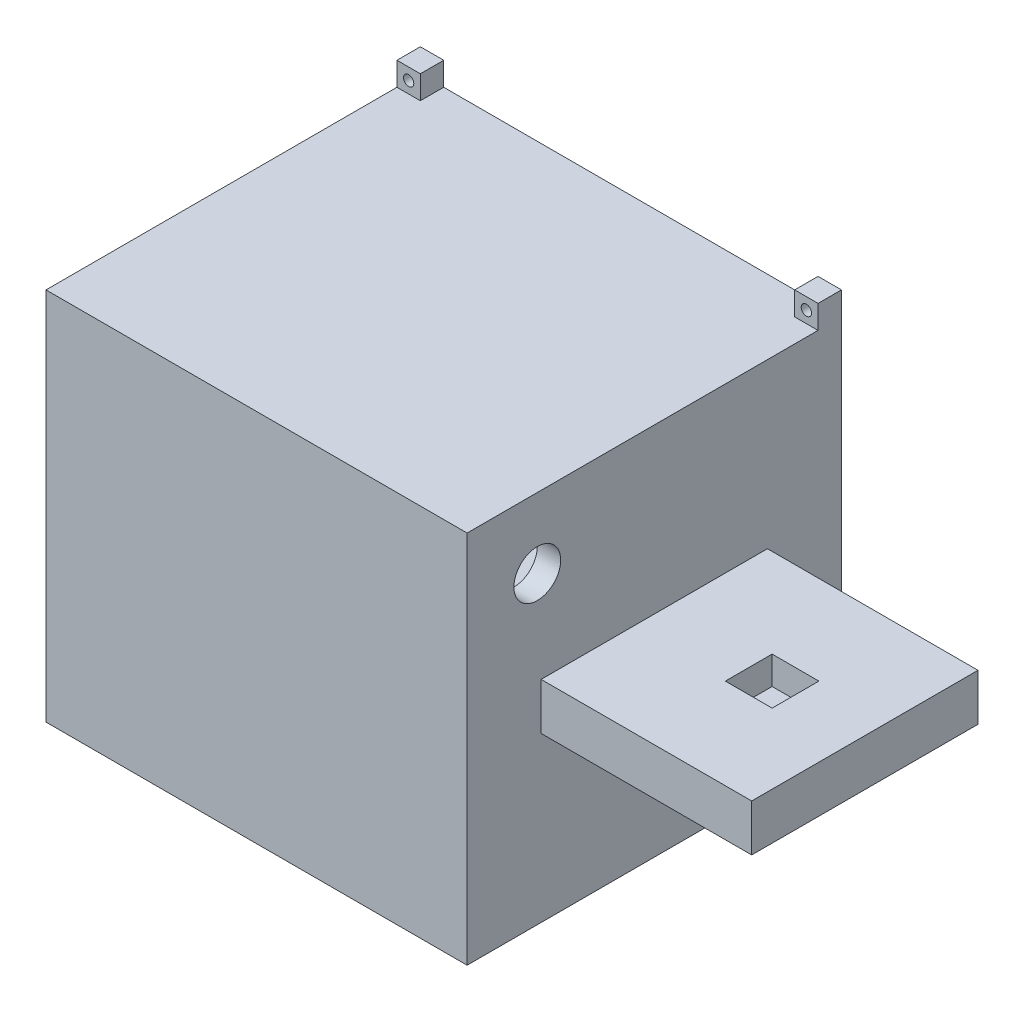
SolidWorks part; units mm, degrees
ref_plane "前基準面" through (0, 0, 0) normal (0, 0, 1) x (1, 0, 0)
ref_plane "上基準面" through (0, 0, 0) normal (0, 1, 0) x (1, 0, 0)
ref_plane "右基準面" through (0, 0, 0) normal (1, 0, 0) x (0, 0, -1)
sketch "草圖1" plane through (0, 0, 0) normal (0, 0, 1) x (1, 0, 0)
  line L0 (-75.5089, 45.5899) -> (59.4911, 45.5899)
  line L4 (-75.5089, 5.5899) -> (59.4911, 5.5899) construction
  line L5 (-75.5089, 45.5899) -> (-75.5089, -34.4101)
  line L6 (59.4911, 45.5899) -> (59.4911, -34.4101)
  line L7 (-75.5089, -34.4101) -> (59.4911, -34.4101)
  dimension "D1" = 135
  dimension "D2" = 80
extrude "填料-伸長1" add sketch "草圖1" along normal blind 80
sketch "草圖5" plane through (0, -34.4101, 0) normal (0, -1, 0) x (1, 0, 0)
  line L0 (14.4911, 80) -> (14.4911, 0)
  line L1 (-75.5089, 80) -> (59.4911, 80) construction
  line L2 (-75.5089, 0) -> (59.4911, 0) construction
  line L3 (14.4911, 0) -> (59.4911, 0)
  line L4 (59.4911, 0) -> (59.4911, 80)
  line L5 (59.4911, 80) -> (14.4911, 80)
  dimension "D1" = 45
sketch "草圖6" plane through (0, 45.5899, 0) normal (0, 1, 0) x (1, 0, 0)
  line L0 (14.4911, 0) -> (14.4911, -80)
  line L1 (14.4911, -80) -> (59.4911, -80)
  line L2 (59.4911, -80) -> (59.4911, 0)
  line L3 (59.4911, 0) -> (14.4911, 0)
extrude "除料-伸長1" cut sketch "草圖6" against normal blind 35
extrude "除料-伸長2" cut sketch "草圖5" against normal blind 35
sketch "草圖7" plane through (0, 0, 0) normal (0, 0, 1) x (1, 0, 0)
  line L0 (-75.5089, 5.5899) -> (59.4911, 5.5899) construction
  line L1 (-75.5089, 45.5899) -> (-75.5089, -34.4101) construction
  line L2 (59.4911, 0.5899) -> (59.4911, 10.5899) construction
  line L3 (-70.5089, -29.4101) -> (-70.5089, 40.5899)
  line L4 (-70.5089, 40.5899) -> (9.4911, 40.5899)
  line L5 (9.4911, 40.5899) -> (9.4911, -29.4101)
  line L6 (-70.5089, -29.4101) -> (9.4911, -29.4101)
  line L7 (14.4911, 45.5899) -> (-75.5089, 45.5899) construction
  line L8 (14.4911, 0.5899) -> (14.4911, -34.4101) construction
  point P11 (9.4911, 5.5899)
  point P12 (-70.5089, 5.5899)
  dimension "D1" = 5
  dimension "D2" = 5
  dimension "D3" = 5
extrude "除料-伸長3" cut sketch "草圖7" along normal blind 75
sketch "草圖8" plane through (0, 0, 0) normal (0, 0, -1) x (-1, 0, 0)
  line L0 (-59.4911, 5.5899) -> (75.5089, 5.5899) construction
  line L1 (-59.4911, 0.5899) -> (-59.4911, 10.5899) construction
  line L2 (75.5089, 45.5899) -> (75.5089, -34.4101) construction
  line L3 (-13.3911, 44.4899) -> (-13.3911, -33.3101)
  line L4 (-13.3911, 44.4899) -> (74.4089, 44.4899)
  line L5 (74.4089, 44.4899) -> (74.4089, -33.3101)
  line L7 (71.6089, -30.5101) -> (71.6089, 41.6899)
  line L8 (71.6089, 41.6899) -> (-10.5911, 41.6899)
  line L9 (-10.5911, 41.6899) -> (-10.5911, -30.5101)
  line L11 (-14.4911, 45.5899) -> (75.5089, 45.5899) construction
  line L12 (-14.4911, 10.5899) -> (-14.4911, 45.5899) construction
  line L13 (71.6089, -30.5101) -> (-10.5911, -30.5101)
  line L14 (-13.3911, -33.3101) -> (74.4089, -33.3101)
  dimension "D1" = 2.8
  dimension "D2" = 2.8
  dimension "D3" = 2.8
  dimension "D4" = 1.1
  dimension "D5" = 1.1
  dimension "D6" = 1.1
extrude "除料-伸長4" cut sketch "草圖8" against normal blind 10
ref_plane "平面1" through (14.4911, 0, 0) normal (1, 0, 0) x (0, 0, -1)
sketch "草圖9" plane through (14.4911, 0, 0) normal (1, 0, 0) x (0, 0, -1)
  line L0 (-80, 5.5899) -> (0, 5.5899) construction
  line L1 (-80, 0.5899) -> (-80, 10.5899) construction
  line L2 (0, 0.5899) -> (0, 10.5899) construction
  line L3 (0, 41.6899) -> (0, -30.5101) construction
  line L4 (-80, 10.5899) -> (-80, 45.5899) construction
  line L5 (0, 10.5899) -> (-80, 10.5899) construction
  line L6 (0, 0.5899) -> (-80, 0.5899) construction
  circle A2 centre (-65, 30.5899) radius 5
  circle A3 centre (-20, -19.4101) radius 5
  dimension "D1" = 10
  dimension "D2" = 10
  dimension "D3" = 20
  dimension "D4" = 15
  dimension "D5" = 20
  dimension "D6" = 20
extrude "除料-伸長5" cut sketch "草圖9" against normal blind 32.4
ref_plane "平面2" through (0, -34.4101, 0) normal (0, -1, 0) x (-1, 0, 0)
sketch "草圖10" plane through (0, -34.4101, 0) normal (0, -1, 0) x (-1, 0, 0)
  line L0 (75.5089, 0) -> (-14.4911, 0) construction
  line L1 (14.0089, -15) -> (35.5089, -15)
  line L2 (14.0089, -15) -> (14.0089, -30)
  line L3 (14.0089, -30) -> (35.5089, -30)
  line L4 (35.5089, -15) -> (35.5089, -30)
  line L5 (75.5089, -80) -> (75.5089, 0) construction
  point P6 (24.7589, -15)
  dimension "D1" = 21.5
  dimension "D2" = 15
  dimension "D3" = 15
  dimension "D4" = 40
extrude "除料-伸長6" cut sketch "草圖10" against normal blind 10
sketch "草圖12" plane through (14.4911, 0, 0) normal (1, 0, 0) x (0, 0, -1)
  line L0 (-40, 45.5899) -> (-40, -34.4101) construction
  line L1 (0, 45.5899) -> (-80, 45.5899) construction
  line L2 (-80, -34.4101) -> (0, -34.4101) construction
  line L3 (-80, 10.5899) -> (-80, 0.5899)
  line L4 (-80, 0.5899) -> (-64.1831, 0.5899)
  line L5 (0, 0.5899) -> (-80, 0.5899) construction
  line L6 (-64.1831, 0.5899) -> (-64.1831, 10.5899)
  line L7 (0, 10.5899) -> (-80, 10.5899) construction
  line L8 (-64.1831, 10.5899) -> (-80, 10.5899)
  line L9 (-15.8169, 10.5899) -> (0, 10.5899)
  line L10 (0, 10.5899) -> (0, 0.5899)
  line L11 (0, 0.5899) -> (-15.8169, 0.5899)
  line L12 (-15.8169, 0.5899) -> (-15.8169, 10.5899)
extrude "除料-伸長7" cut sketch "草圖12" along normal blind 45
ref_plane "平面3" through (0, 0.5899, 0) normal (0, -1, 0) x (-1, 0, 0)
sketch "草圖14" plane through (0, 0.5899, 0) normal (0, -1, 0) x (-1, 0, 0)
  line L4 (-59.4911, -40) -> (-70.9929, -40) construction
  line L5 (-59.4911, -15.8169) -> (-59.4911, -64.1831) construction
  line L6 (-38.0091, -35.1028) -> (-21.5179, -38.5)
  line L7 (-38.0091, -44.8972) -> (-21.5179, -41.5)
  line L8 (-39.0179, -45) -> (-39.0179, -45.1799) construction
  line L9 (-40.0267, -44.8972) -> (-56.5179, -41.5)
  line L10 (-40.0267, -35.1028) -> (-56.5179, -38.5)
  line L11 (-49.9929, -40) -> (-38.9929, -40) construction
  line L12 (-20.0179, -40) -> (-28.4331, -40) construction
  arc A2 (-40.0267, -44.8972) -> (-38.0091, -44.8972) centre (-39.0179, -40) ccw
  arc A3 (-21.5179, -41.5) -> (-21.5179, -38.5) centre (-21.5179, -40) ccw
  arc A5 (-56.5179, -41.5) -> (-56.5179, -38.5) centre (-56.5179, -40) cw
  arc A6 (-38.0091, -35.1028) -> (-40.0267, -35.1028) centre (-39.0179, -40) ccw
  dimension "D1" = 10
  dimension "D2" = 3
extrude "除料-伸長8" cut sketch "草圖14" against normal blind 3
ref_plane "平面4" through (0, 10.5899, 0) normal (0, 1, 0) x (1, 0, 0)
sketch "草圖15" plane through (0, 10.5899, 0) normal (0, 1, 0) x (1, 0, 0)
  line L0 (14.4911, -15.8169) -> (14.4911, -64.1831) construction
  line L1 (34.4911, -34.8169) -> (44.4911, -34.8169)
  line L2 (34.4911, -34.8169) -> (34.4911, -44.8169)
  line L3 (34.4911, -44.8169) -> (44.4911, -44.8169)
  line L4 (44.4911, -34.8169) -> (44.4911, -44.8169)
  line L5 (59.4911, -15.8169) -> (14.4911, -15.8169) construction
  dimension "D1" = 10
  dimension "D2" = 10
  dimension "D3" = 20
  dimension "D4" = 19
extrude "除料-伸長9" cut sketch "草圖15" against normal blind 6
sketch "草圖17" plane through (0, 0.5899, 0) normal (0, -1, 0) x (-1, 0, 0)
  line L0 (-58.0179, -40) -> (-20.0179, -40) construction
  line L1 (-39.0179, -45) -> (-39.0179, -35) construction
  arc A0 (-56.5179, -38.5) -> (-56.5179, -41.5) centre (-56.5179, -40) ccw construction
  arc A1 (-21.5179, -41.5) -> (-21.5179, -38.5) centre (-21.5179, -40) ccw construction
  arc A2 (-40.0267, -44.8972) -> (-38.0091, -44.8972) centre (-39.0179, -40) ccw construction
  arc A3 (-38.0091, -35.1028) -> (-40.0267, -35.1028) centre (-39.0179, -40) ccw construction
  circle A4 centre (-39.0179, -40) radius 1.0953
extrude "除料-伸長11" cut sketch "草圖17" against normal blind 7
sketch "草圖18" plane through (0, 0, 0) normal (0, 0, 1) x (1, 0, 0)
  line L0 (59.4911, 5.5899) -> (-75.5089, 5.5899) construction
  line L1 (59.4911, 10.5899) -> (59.4911, 0.5899) construction
  line L2 (-75.5089, 45.5899) -> (-75.5089, -34.4101) construction
  line L3 (14.4911, 45.5899) -> (-75.5089, 45.5899) construction
  line L4 (-30.5089, 45.5899) -> (-30.5089, -34.4101) construction
  line L5 (-44, -34.4101) -> (44, -34.4101) construction
  line L6 (14.4911, -43.147) -> (14.4911, 43.147) construction
  line L7 (14.4911, 45.5899) -> (9.4911, 45.5899)
  line L8 (14.4911, 45.5899) -> (14.4911, 50.5899)
  line L9 (14.4911, 50.5899) -> (9.4911, 50.5899)
  line L10 (9.4911, 45.5899) -> (9.4911, 50.5899)
  line L11 (14.4911, 48.0899) -> (9.4911, 48.0899) construction
  line L12 (11.9911, 50.5899) -> (11.9911, 45.5899) construction
  line L13 (-75.5089, 50.5899) -> (-70.5089, 50.5899)
  line L14 (-70.5089, 45.5899) -> (-70.5089, 50.5899)
  line L15 (-75.5089, 45.5899) -> (-70.5089, 45.5899)
  line L16 (-75.5089, 45.5899) -> (-75.5089, 50.5899)
  line L17 (-75.5089, -34.4101) -> (-70.5089, -34.4101)
  line L18 (-75.5089, -34.4101) -> (-75.5089, -39.4101)
  line L19 (-75.5089, -39.4101) -> (-70.5089, -39.4101)
  line L20 (-70.5089, -34.4101) -> (-70.5089, -39.4101)
  line L21 (14.4911, -34.4101) -> (9.4911, -34.4101)
  line L22 (9.4911, -34.4101) -> (9.4911, -39.4101)
  line L23 (14.4911, -39.4101) -> (9.4911, -39.4101)
  line L24 (14.4911, -34.4101) -> (14.4911, -39.4101)
  circle A0 centre (11.9911, 48.0899) radius 1.1
  circle A1 centre (-73.0089, 48.0899) radius 1.1
  circle A2 centre (-73.0089, -36.9101) radius 1.1
  circle A3 centre (11.9911, -36.9101) radius 1.1
  dimension "D3" = 2.2
  dimension "D1" = 5
  dimension "D2" = 5
extrude "填料-伸長2" add sketch "草圖18" along normal blind 5
